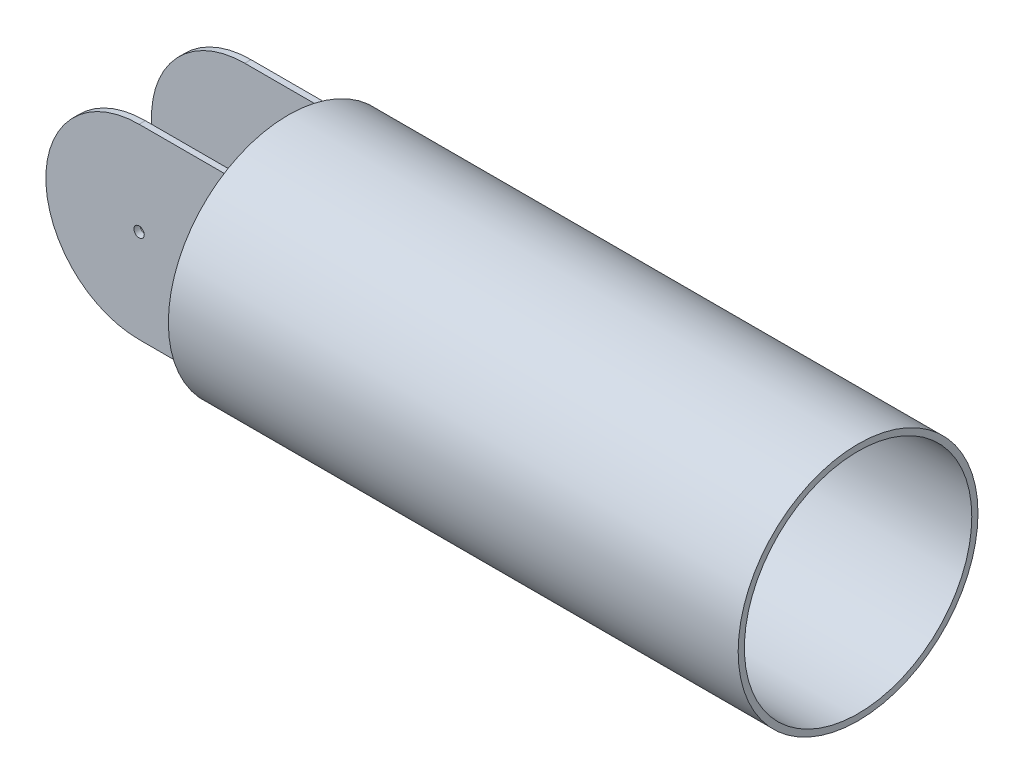
SolidWorks part; units mm, degrees
ref_plane "Ön Düzlem" through (0, 0, 0) normal (0, 0, 1) x (1, 0, 0)
ref_plane "Üst Düzlem" through (0, 0, 0) normal (0, 1, 0) x (1, 0, 0)
ref_plane "Sağ Düzlem" through (0, 0, 0) normal (1, 0, 0) x (0, 0, -1)
sketch "Çizim10" plane through (0, 0, 0) normal (0, 0, 1) x (1, 0, 0)
  line L1 (0, 0) -> (180, 0)
  line L2 (0, 0) -> (0, 180)
  line L3 (0, 180) -> (180, 180)
  line L4 (180, 0) -> (180, 180)
  dimension "D1" = 180
  dimension "D2" = 180
extrude "Yükseklik-Ekstrüzyon1" add sketch "Çizim10" along normal blind 108
sketch "Çizim11" plane through (0, 0, 108) normal (0, 0, 1) x (1, 0, 0)
  line L0 (90, 180) -> (0, 180)
  line L1 (0, 180) -> (0, 0)
  line L2 (0, 0) -> (90, 0)
  circle A0 centre (90, 90) radius 90
  line M1 (0, 180) -> (0, 0)
  line M2 (0, 0) -> (180, 0)
  line M4 (180, 180) -> (0, 180)
extrude "Kes-Ekstrüzyon7" cut sketch "Çizim11" against normal blind 108 contours A0 M4 M1 | A0 L1 M2
sketch "Çizim13" plane through (180, 0, 0) normal (1, 0, 0) x (0, 0, -1)
  circle A0 centre (-54, 90) radius 115.75
  dimension "D1" = 231.5
extrude "Yükseklik-Ekstrüzyon2" add sketch "Çizim13" along normal blind 550
sketch "Çizim14" plane through (730, 0, 0) normal (1, 0, 0) x (0, 0, -1)
  circle A0 centre (-54, 90) radius 109.75
  circle A1 centre (-54, 90) radius 115.75 construction
  dimension "D1" = 6
extrude "Kes-Ekstrüzyon8" cut sketch "Çizim14" against normal blind 294
sketch "Çizim15" plane through (0, 180, 0) normal (0, 1, 0) x (1, 0, 0)
  line L0 (180, 61.75) -> (180, -169.75) construction
  line L1 (180, -6) -> (0, -6)
  line L2 (180, -6) -> (180, -102)
  line L3 (180, -102) -> (0, -102)
  line L4 (0, -6) -> (0, -102)
  line L5 (0, 0) -> (0, -108) construction
  line L7 (180, 0) -> (90, 0) construction
  line L8 (180, -108) -> (90, -108) construction
  dimension "D1" = 6
  dimension "D2" = 6
extrude "Kes-Ekstrüzyon9" cut sketch "Çizim15" against normal blind 294
sketch "Çizim16" plane through (0, 0, 108) normal (0, 0, 1) x (1, 0, 0)
  circle A0 centre (90, 90) radius 5
  dimension "D1" = 10
extrude "Kes-Ekstrüzyon10" cut sketch "Çizim16" against normal blind 294
